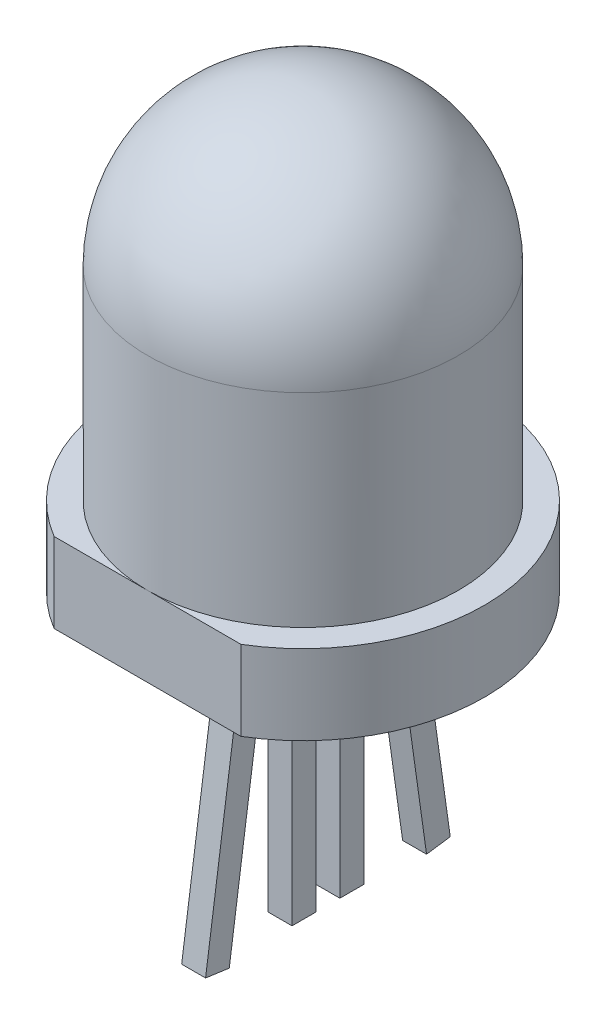
SolidWorks part; units mm, degrees
ref_plane "Plan de face" through (0, 0, 0) normal (0, 0, 1) x (1, 0, 0)
ref_plane "Plan de dessus" through (0, 0, 0) normal (0, 1, 0) x (1, 0, 0)
ref_plane "Plan de droite" through (0, 0, 0) normal (1, 0, 0) x (0, 0, -1)
sketch "Esquisse1" plane through (0, 0, 0) normal (0, 1, 0) x (1, 0, 0)
  circle A0 centre (0, 0) radius 3.9
  dimension "D1" = 7.8
extrude "Boss.-Extru.1" add sketch "Esquisse1" along normal blind 9
fillet "Congé1" radius 3.9 1 edges at (0, 9, 3.9)
sketch "Esquisse2" plane through (0, 0, 0) normal (0, -1, 0) x (1, 0, 0)
  line L1 (2.3436, 3.9) -> (-2.3436, 3.9)
  arc A0 (-2.3436, 3.9) -> (2.3436, 3.9) centre (0, 0) ccw
  circle A2 centre (0, 0) radius 3.9 construction
  dimension "D1" = 9.1
extrude "Boss.-Extru.2" add sketch "Esquisse2" along normal blind 2
sketch "Esquisse3" plane through (0, -2, 0) normal (0, -1, 0) x (1, 0, 0)
  line L0 (0, 3.9) -> (0, -4.55) construction
  line L1 (2.3436, 3.9) -> (-2.3436, 3.9) construction
  line L2 (0, -0.625) -> (0, -1.225) construction
  line L3 (-0.3, -0.025) -> (0.3, -0.025)
  line L4 (-0.3, -0.025) -> (-0.3, 0.575)
  line L5 (-0.3, 0.575) -> (0.3, 0.575)
  line L6 (0.3, -0.025) -> (0.3, 0.575)
  line L7 (0.3, -1.225) -> (-0.3, -1.225)
  line L8 (0.3, -1.225) -> (0.3, -0.625)
  line L9 (0.3, -0.625) -> (-0.3, -0.625)
  line L10 (-0.3, -1.225) -> (-0.3, -0.625)
  line L11 (0, -0.025) -> (0, 0.575) construction
  line L12 (0, -0.025) -> (0, -0.625) construction
  line L13 (-0.3, -0.025) -> (-0.3, -0.625) construction
  line L14 (-0.3, -0.325) -> (0, -0.325) construction
  arc A0 (-2.3436, 3.9) -> (2.3436, 3.9) centre (0, 0) ccw construction
  point P17 (0, -0.925)
  point P20 (0, 0.275)
  point P21 (0, 0.275)
  point P22 (0, -0.925)
  point P25 (0, -0.325)
  dimension "D1" = 1.2
  dimension "D2" = 0.6
  dimension "D3" = 0.6
  dimension "D4" = 0.6
  dimension "D5" = 0.6
extrude "Boss.-Extru.3" add sketch "Esquisse3" along normal blind 6.8
sketch "Esquisse5" plane through (0, -2, 0) normal (0, -1, 0) x (1, 0, 0)
  line L0 (0, 3.9) -> (0, 0.575) construction
  line L1 (2.3436, 3.9) -> (-2.3436, 3.9) construction
  line L2 (0.3, 0.575) -> (-0.3, 0.575) construction
  line L3 (-0.4685, 1.175) -> (0.4478, 1.175) construction
  dimension "D1" = 0.6
ref_plane "Plan1" through (0, -2.1232, 0.2984) normal (0, -0.9903, 0.1392) x (-1, 0, 0)
sketch "Esquisse6" plane through (0, -2.1232, 0.2984) normal (0, -0.9903, 0.1392) x (-1, 0, 0)
  line L0 (0.4685, -0.8852) -> (-0.4478, -0.8852) construction
  line L1 (-0.3, -0.8852) -> (0.3, -0.8852)
  line L2 (-0.3, -0.8852) -> (-0.3, -1.4852)
  line L3 (-0.3, -1.4852) -> (0.3, -1.4852)
  line L4 (0.3, -0.8852) -> (0.3, -1.4852)
  line L5 (0, -0.8852) -> (0, -1.4852) construction
  line L6 (0, -3.5837) -> (0, -0.2911) construction
  point P8 (0, -1.1852)
  point P9 (0, -1.1852)
  dimension "D1" = 0.6
  dimension "D2" = 0.6
extrude "Boss.-Extru.4" add sketch "Esquisse6" along normal blind 7
sketch "Esquisse7" plane through (0, -2, 0) normal (0, -1, 0) x (1, 0, 0)
  line L0 (0, -1.225) -> (0, -4.55) construction
  line L1 (-0.3, -1.225) -> (0.3, -1.225) construction
  line L2 (-0.3695, -1.825) -> (0.3997, -1.825) construction
  arc A0 (-2.3436, 3.9) -> (2.3436, 3.9) centre (0, 0) ccw construction
  dimension "D1" = 0.6
ref_plane "Plan2" through (0, -2.2128, -0.311) normal (0, -0.9903, -0.1392) x (-1, 0, 0)
sketch "Esquisse8" plane through (0, -2.2128, -0.311) normal (0, -0.9903, -0.1392) x (-1, 0, 0)
  line L0 (0, 2.1289) -> (0, 1.5289) construction
  line L1 (-0.3, 1.5289) -> (0.3, 1.5289)
  line L2 (-0.3, 1.5289) -> (-0.3, 2.1289)
  line L3 (-0.3, 2.1289) -> (0.3, 2.1289)
  line L4 (0.3, 1.5289) -> (0.3, 2.1289)
  line L5 (0, 0.9347) -> (0, 4.2274) construction
  point P7 (0, 1.8289)
  dimension "D1" = 0.6
  dimension "D2" = 0.6
extrude "Boss.-Extru.5" add sketch "Esquisse8" along normal blind 7
